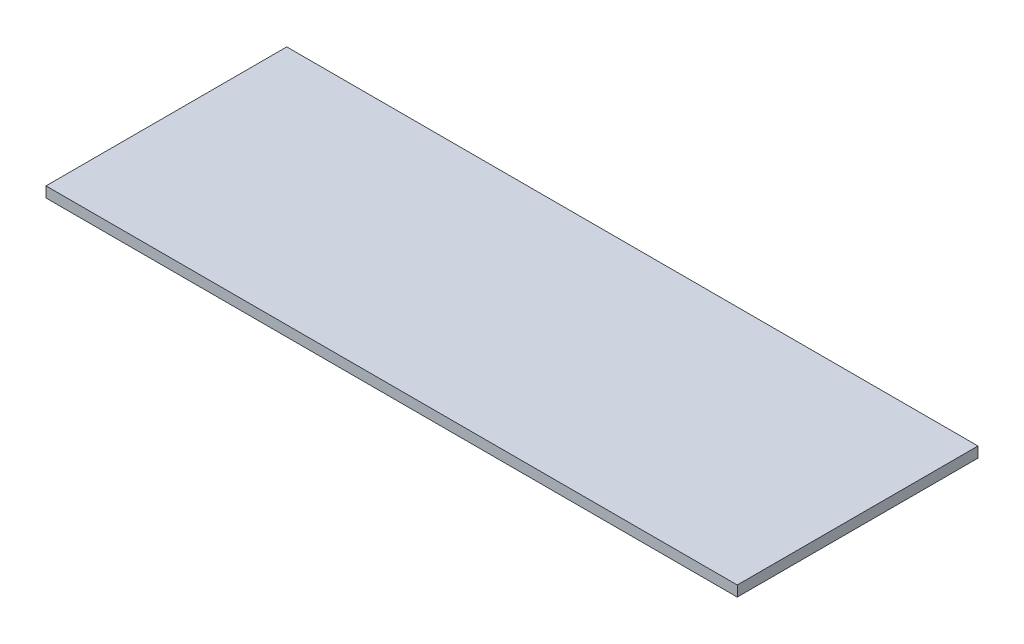
SolidWorks part; units mm, degrees
ref_plane "Front Plane" through (0, 0, 0) normal (0, 0, 1) x (1, 0, 0)
ref_plane "Top Plane" through (0, 0, 0) normal (0, 1, 0) x (1, 0, 0)
ref_plane "Right Plane" through (0, 0, 0) normal (1, 0, 0) x (0, 0, -1)
sketch "Sketch1" plane through (0, 0, 0) normal (0, 1, 0) x (1, 0, 0)
  line L0 (-134.925, 0) -> (65.075, 0) construction
  line L1 (134.925, -46.99) -> (-134.925, -46.99)
  line L2 (134.925, -46.99) -> (134.925, 46.99)
  line L3 (134.925, 46.99) -> (-134.925, 46.99)
  line L4 (-134.925, -46.99) -> (-134.925, 46.99)
  line L5 (134.925, -46.99) -> (-134.925, 46.99) construction
  line L6 (134.925, 46.99) -> (-134.925, -46.99) construction
  point P0 (0, 0)
  dimension "D1" = 93.98
  dimension "D2" = 69.85
  dimension "D3" = 200
extrude "Boss-Extrude1" add sketch "Sketch1" along normal blind 4.11
